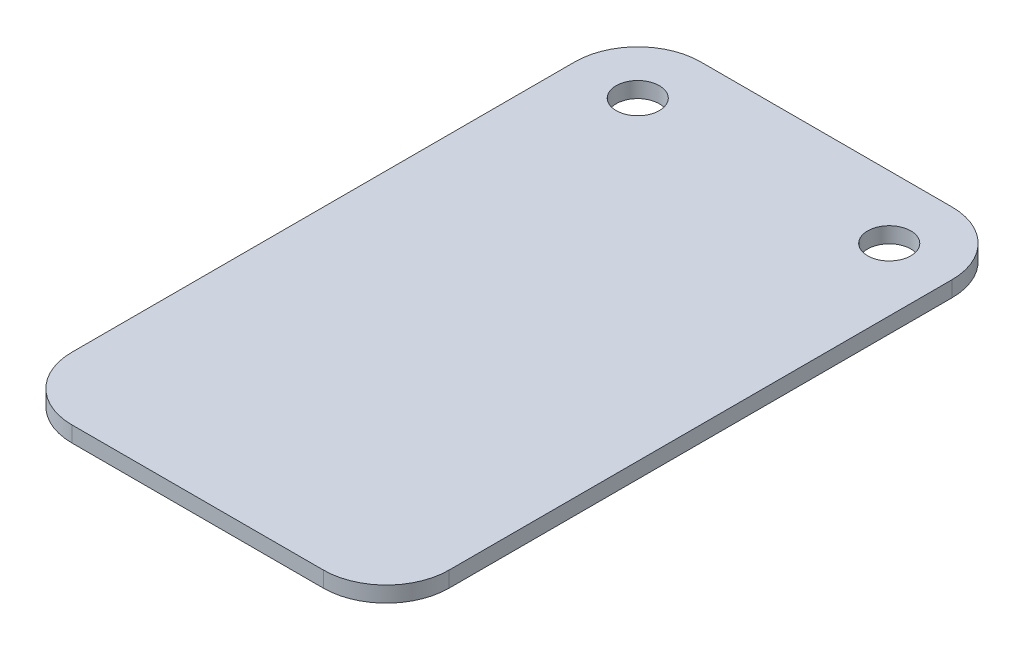
SolidWorks part; units mm, degrees
ref_plane "Front Plane" through (0, 0, 0) normal (0, 0, 1) x (1, 0, 0)
ref_plane "Top Plane" through (0, 0, 0) normal (0, 1, 0) x (1, 0, 0)
ref_plane "Right Plane" through (0, 0, 0) normal (1, 0, 0) x (0, 0, -1)
sketch "Sketch1" plane through (0, 0, 0) normal (0, 1, 0) x (1, 0, 0)
  line L1 (6.35, 0) -> (31.75, 0)
  line L2 (0, 6.35) -> (0, 57.15)
  line L3 (6.35, 63.5) -> (31.75, 63.5)
  line L4 (38.1, 6.35) -> (38.1, 57.15)
  circle A2 centre (31.75, 57.15) radius 2.1828
  circle A3 centre (6.35, 57.15) radius 2.1828
  arc A4 (6.35, 63.5) -> (0, 57.15) centre (6.35, 57.15) ccw
  arc A5 (38.1, 57.15) -> (31.75, 63.5) centre (31.75, 57.15) ccw
  arc A6 (6.35, 0) -> (0, 6.35) centre (6.35, 6.35) cw
  arc A7 (38.1, 6.35) -> (31.75, 0) centre (31.75, 6.35) cw
  point P19 (0, 0)
  dimension "D5" = 4.3656
  dimension "D8" = 4.3656
  dimension "D15" = 6.35
  dimension "D16" = 6.35
  dimension "D17" = 6.35
  dimension "D18" = 6.35
  dimension "D1" = 38.1
  dimension "D2" = 63.5
  dimension "D3" = 6.35
  dimension "D4" = 6.35
  dimension "D6" = 6.35
  dimension "D7" = 6.35
extrude "Boss-Extrude1" add sketch "Sketch1" along normal blind 1.5875
